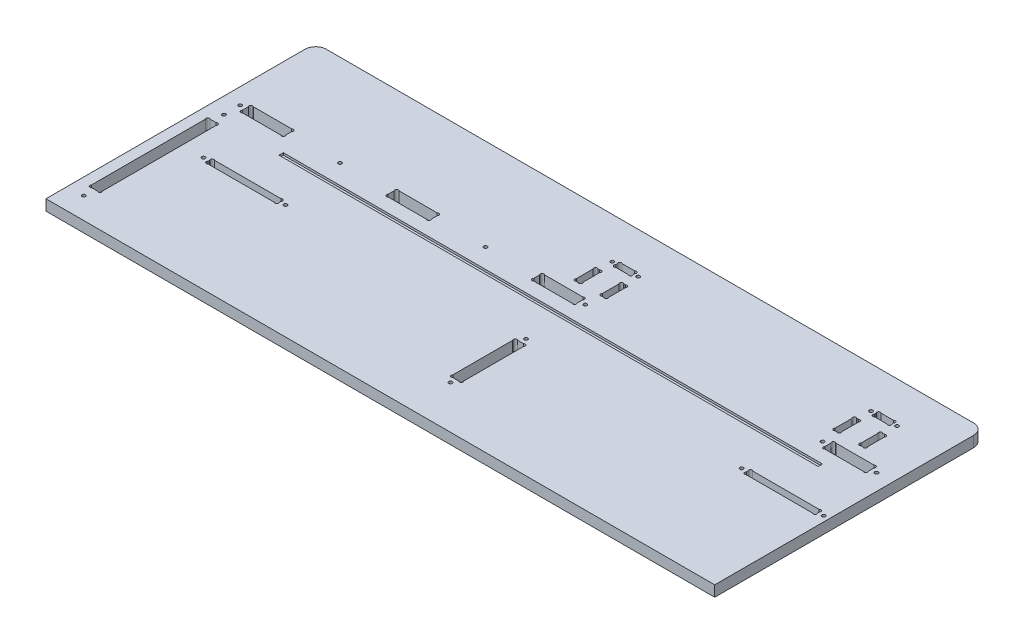
SolidWorks part; units mm, degrees
ref_plane "Plan de face" through (0, 0, 0) normal (0, 0, 1) x (1, 0, 0)
ref_plane "Plan de dessus" through (0, 0, 0) normal (0, 1, 0) x (1, 0, 0)
ref_plane "Plan de droite" through (0, 0, 0) normal (1, 0, 0) x (0, 0, -1)
sketch "Esquisse1" plane through (0, 0, 0) normal (0, 1, 0) x (1, 0, 0)
  line L0 (-55.9706, 0) -> (688.9813, 0) construction
  line L1 (0, -39.5787) -> (0, 380.8584) construction
  line L2 (-55.9706, 250) -> (688.9813, 250) construction
  line L3 (620, 380.8584) -> (620, -39.5787) construction
  line L4 (-21.2246, 170) -> (673.9823, 170) construction
  line L5 (340, 341.5482) -> (340, -24.8222) construction
  line L6 (673.9823, 160) -> (-21.2246, 160) construction
  line L7 (10, 341.5482) -> (10, -39.5787) construction
  line L8 (20, -39.5787) -> (20, 223.7385) construction
  line L9 (610, 341.5482) -> (610, 124.8557) construction
  line L10 (550, 341.5482) -> (550, 124.8557) construction
  line L11 (49.0204, 10) -> (-38.752, 10) construction
  line L12 (244.0085, 215) -> (592.9306, 215) construction
  line L13 (580, 280.9066) -> (580, 124.8557) construction
  line L14 (310, 280.9066) -> (310, 124.8557) construction
  line L15 (445, 234.3834) -> (445, 341.5482) construction
  line L16 (290.8762, 209) -> (347.4261, 209) construction
  line L17 (316, 236.8233) -> (316, 163.128) construction
  line L18 (334, 236.8233) -> (334, 163.128) construction
  line L19 (325, 257.541) -> (325, 197.6776) construction
  line L20 (313, 223.7385) -> (313, 205.81) construction
  line L21 (306.3451, 212) -> (359.8928, 212) construction
  line L22 (318.7842, 189.5) -> (359.8928, 189.5) construction
  line L23 (317, 223.7385) -> (317, 206.607) construction
  line L24 (306.3451, 179.5) -> (325, 179.5) construction
  line L25 (316, 179.5) -> (298.4851, 197.0149) construction
  line L26 (317, 211.2627) -> (317, 212.7373)
  line L27 (317, 215) -> (329.8508, 202.1492) construction
  line L28 (319.2627, 215) -> (330.7373, 215)
  line L29 (333, 211.2627) -> (333, 212.7373)
  line L30 (330.7373, 209) -> (319.2627, 209)
  line L31 (312.2627, 179.5) -> (313.7373, 179.5)
  line L32 (312.2627, 199.5) -> (313.7373, 199.5)
  line L33 (310, 197.2373) -> (310, 181.7627)
  line L34 (316, 181.7627) -> (316, 197.2373)
  line L35 (334, 181.7627) -> (334, 197.2373)
  line L36 (340, 197.2373) -> (340, 181.7627)
  line L37 (337.7373, 199.5) -> (336.2627, 199.5)
  line L38 (337.7373, 179.5) -> (336.2627, 179.5)
  line L39 (552.2627, 179.5) -> (553.7373, 179.5)
  line L40 (552.2627, 199.5) -> (553.7373, 199.5)
  line L41 (550, 197.2373) -> (550, 181.7627)
  line L42 (556, 181.7627) -> (556, 197.2373)
  line L43 (574, 181.7627) -> (574, 197.2373)
  line L44 (580, 197.2373) -> (580, 181.7627)
  line L45 (577.7373, 199.5) -> (576.2627, 199.5)
  line L46 (577.7373, 179.5) -> (576.2627, 179.5)
  line L47 (559.2627, 209) -> (570.7373, 209)
  line L48 (557, 211.2627) -> (557, 212.7373)
  line L49 (570.7373, 215) -> (559.2627, 215)
  line L50 (573, 211.2627) -> (573, 212.7373)
  line L51 (80.4661, 165) -> (624.1581, 165) construction
  line L52 (560, 174.5066) -> (560, 138.2607) construction
  line L53 (555, 174.5066) -> (555, 138.2607) construction
  line L54 (560, 160) -> (573.9521, 173.9521) construction
  line L55 (560, 167.7373) -> (560, 162.2627)
  line L56 (600, 167.7373) -> (600, 162.2627)
  line L57 (562.2627, 170) -> (597.7373, 170)
  line L58 (597.7373, 160) -> (562.2627, 160)
  line L59 (292.2627, 160) -> (327.7373, 160)
  line L60 (327.7373, 170) -> (292.2627, 170)
  line L61 (290, 167.7373) -> (290, 162.2627)
  line L62 (330, 167.7373) -> (330, 162.2627)
  line L63 (175, 313.2866) -> (175, 124.8557) construction
  line L64 (20, 167.7373) -> (20, 162.2627)
  line L65 (60, 167.7373) -> (60, 162.2627)
  line L66 (22.2627, 170) -> (57.7373, 170)
  line L67 (57.7373, 160) -> (22.2627, 160)
  line L68 (155, 179.5) -> (155, 124.8557) construction
  line L69 (155, 160) -> (177.234, 182.234) construction
  line L70 (155, 167.7373) -> (155, 162.2627)
  line L71 (195, 167.7373) -> (195, 162.2627)
  line L72 (157.2627, 170) -> (192.7373, 170)
  line L73 (192.7373, 160) -> (157.2627, 160)
  line L74 (242.5, 124.8557) -> (242.5, 179.5) construction
  line L75 (-16.8838, 85) -> (49.0204, 85) construction
  line L76 (10, 250) -> (610, 250)
  line L77 (0, 240) -> (0, 0)
  line L78 (0, 0) -> (620, 0)
  line L79 (620, 240) -> (620, 0)
  line L80 (28.427, 30) -> (-7.473, 30) construction
  line L81 (4.5525, 20) -> (28.427, 20) construction
  line L82 (15, 149.0553) -> (15, -13.6747) construction
  line L83 (20, 30) -> (-3.7272, 53.7272) construction
  line L84 (12.2627, 30) -> (17.7373, 30)
  line L85 (12.2627, 140) -> (17.7373, 140)
  line L86 (10, 137.7373) -> (10, 32.2627)
  line L87 (20, 32.2627) -> (20, 137.7373)
  line L88 (673.9823, 109) -> (-21.2246, 109) construction
  line L89 (673.9823, 103) -> (-21.2246, 103) construction
  line L90 (330, -24.8222) -> (330, 122.6364) construction
  line L91 (356.2719, 115) -> (325, 115) construction
  line L92 (356.2719, 35) -> (308.6408, 35) construction
  line L93 (335, 32.2627) -> (335, 82.0162) construction
  line L94 (345.0286, 75) -> (308.6408, 75) construction
  line L95 (345.0286, 45) -> (316, 45) construction
  line L96 (345.0286, 40) -> (333, 40) construction
  line L97 (330, 45) -> (340.0199, 55.0199) construction
  line L98 (337.7373, 45) -> (332.2627, 45)
  line L99 (337.7373, 105) -> (332.2627, 105)
  line L100 (340, 47.2627) -> (340, 102.7373)
  line L101 (330, 102.7373) -> (330, 47.2627)
  line L102 (35, 95.2987) -> (35, 134.8153) construction
  line L103 (327.5, -33.1463) -> (327.5, -9.4075) construction
  line L104 (577, 83.0157) -> (577, 115) construction
  line L105 (610, 83.0157) -> (610, 115) construction
  line L106 (641.1197, 106) -> (607.2136, 106) construction
  line L107 (615, 100.9312) -> (615, 118.2543) construction
  line L108 (610, 103) -> (596.866, 116.134) construction
  line L109 (610, 105.2627) -> (610, 106.7373)
  line L110 (544, 105.2627) -> (544, 106.7373)
  line L111 (607.7373, 103) -> (546.2627, 103)
  line L112 (546.2627, 109) -> (607.7373, 109)
  line L113 (108.7373, 109) -> (47.2627, 109)
  line L114 (47.2627, 103) -> (108.7373, 103)
  line L115 (111, 105.2627) -> (111, 106.7373)
  line L116 (45, 105.2627) -> (45, 106.7373)
  arc A0 (319.2627, 215) -> (317, 212.7373) centre (318.1314, 213.8686) ccw
  arc A1 (319.2627, 209) -> (317, 211.2627) centre (318.1314, 210.1314) cw
  arc A2 (330.7373, 209) -> (333, 211.2627) centre (331.8686, 210.1314) ccw
  arc A3 (330.7373, 215) -> (333, 212.7373) centre (331.8686, 213.8686) cw
  arc A4 (313.7373, 179.5) -> (316, 181.7627) centre (314.8686, 180.6314) ccw
  arc A5 (312.2627, 179.5) -> (310, 181.7627) centre (311.1314, 180.6314) cw
  arc A6 (312.2627, 199.5) -> (310, 197.2373) centre (311.1314, 198.3686) ccw
  arc A7 (313.7373, 199.5) -> (316, 197.2373) centre (314.8686, 198.3686) cw
  arc A8 (336.2627, 179.5) -> (334, 181.7627) centre (335.1314, 180.6314) cw
  arc A9 (336.2627, 199.5) -> (334, 197.2373) centre (335.1314, 198.3686) ccw
  arc A10 (337.7373, 199.5) -> (340, 197.2373) centre (338.8686, 198.3686) cw
  arc A11 (337.7373, 179.5) -> (340, 181.7627) centre (338.8686, 180.6314) ccw
  arc A12 (552.2627, 179.5) -> (550, 181.7627) centre (551.1314, 180.6314) cw
  arc A13 (552.2627, 199.5) -> (550, 197.2373) centre (551.1314, 198.3686) ccw
  arc A14 (553.7373, 199.5) -> (556, 197.2373) centre (554.8686, 198.3686) cw
  arc A15 (553.7373, 179.5) -> (556, 181.7627) centre (554.8686, 180.6314) ccw
  arc A16 (576.2627, 199.5) -> (574, 197.2373) centre (575.1314, 198.3686) ccw
  arc A17 (577.7373, 199.5) -> (580, 197.2373) centre (578.8686, 198.3686) cw
  arc A18 (577.7373, 179.5) -> (580, 181.7627) centre (578.8686, 180.6314) ccw
  arc A19 (576.2627, 179.5) -> (574, 181.7627) centre (575.1314, 180.6314) cw
  arc A20 (559.2627, 215) -> (557, 212.7373) centre (558.1314, 213.8686) ccw
  arc A21 (559.2627, 209) -> (557, 211.2627) centre (558.1314, 210.1314) cw
  arc A22 (570.7373, 209) -> (573, 211.2627) centre (571.8686, 210.1314) ccw
  arc A23 (570.7373, 215) -> (573, 212.7373) centre (571.8686, 213.8686) cw
  circle A24 centre (313, 212) radius 1.6
  circle A25 centre (337, 212) radius 1.6
  circle A26 centre (553, 212) radius 1.6
  circle A27 centre (577, 212) radius 1.6
  circle A28 centre (555, 165) radius 1.6
  arc A29 (560, 162.2627) -> (562.2627, 160) centre (561.1314, 161.1314) ccw
  arc A30 (560, 167.7373) -> (562.2627, 170) centre (561.1314, 168.8686) cw
  arc A31 (600, 167.7373) -> (597.7373, 170) centre (598.8686, 168.8686) ccw
  arc A32 (600, 162.2627) -> (597.7373, 160) centre (598.8686, 161.1314) cw
  circle A33 centre (605, 165) radius 1.6
  arc A34 (290, 162.2627) -> (292.2627, 160) centre (291.1314, 161.1314) ccw
  arc A35 (290, 167.7373) -> (292.2627, 170) centre (291.1314, 168.8686) cw
  arc A36 (330, 167.7373) -> (327.7373, 170) centre (328.8686, 168.8686) ccw
  arc A37 (330, 162.2627) -> (327.7373, 160) centre (328.8686, 161.1314) cw
  circle A38 centre (335, 165) radius 1.6
  circle A39 centre (15, 165) radius 1.6
  arc A40 (20, 162.2627) -> (22.2627, 160) centre (21.1314, 161.1314) ccw
  arc A41 (20, 167.7373) -> (22.2627, 170) centre (21.1314, 168.8686) cw
  arc A42 (60, 167.7373) -> (57.7373, 170) centre (58.8686, 168.8686) ccw
  arc A43 (60, 162.2627) -> (57.7373, 160) centre (58.8686, 161.1314) cw
  arc A44 (155, 162.2627) -> (157.2627, 160) centre (156.1314, 161.1314) ccw
  arc A45 (155, 167.7373) -> (157.2627, 170) centre (156.1314, 168.8686) cw
  arc A46 (195, 162.2627) -> (192.7373, 160) centre (193.8686, 161.1314) cw
  arc A47 (195, 167.7373) -> (192.7373, 170) centre (193.8686, 168.8686) ccw
  circle A48 centre (242.5, 165) radius 1.6
  circle A49 centre (107.5, 165) radius 1.6
  arc A50 (17.7373, 30) -> (20, 32.2627) centre (18.8686, 31.1314) ccw
  circle A51 centre (15, 20) radius 1.6
  arc A52 (12.2627, 30) -> (10, 32.2627) centre (11.1314, 31.1314) cw
  arc A53 (17.7373, 140) -> (20, 137.7373) centre (18.8686, 138.8686) cw
  arc A54 (12.2627, 140) -> (10, 137.7373) centre (11.1314, 138.8686) ccw
  circle A55 centre (15, 150) radius 1.6
  arc A56 (10, 250) -> (0, 240) centre (10, 240) ccw
  arc A57 (610, 250) -> (620, 240) centre (610, 240) cw
  circle A58 centre (335, 40) radius 1.6
  arc A59 (330, 47.2627) -> (332.2627, 45) centre (331.1314, 46.1314) ccw
  arc A60 (340, 47.2627) -> (337.7373, 45) centre (338.8686, 46.1314) cw
  arc A61 (330, 102.7373) -> (332.2627, 105) centre (331.1314, 103.8686) cw
  arc A62 (340, 102.7373) -> (337.7373, 105) centre (338.8686, 103.8686) ccw
  circle A63 centre (335, 110) radius 1.6
  arc A64 (607.7373, 103) -> (610, 105.2627) centre (608.8686, 104.1314) ccw
  circle A65 centre (615, 106) radius 1.6
  arc A66 (607.7373, 109) -> (610, 106.7373) centre (608.8686, 107.8686) cw
  circle A67 centre (539, 106) radius 1.6
  arc A68 (546.2627, 109) -> (544, 106.7373) centre (545.1314, 107.8686) ccw
  arc A69 (546.2627, 103) -> (544, 105.2627) centre (545.1314, 104.1314) cw
  arc A70 (108.7373, 103) -> (111, 105.2627) centre (109.8686, 104.1314) ccw
  arc A71 (108.7373, 109) -> (111, 106.7373) centre (109.8686, 107.8686) cw
  circle A72 centre (116, 106) radius 1.6
  arc A73 (47.2627, 109) -> (45, 106.7373) centre (46.1314, 107.8686) ccw
  circle A74 centre (40, 106) radius 1.6
  arc A75 (47.2627, 103) -> (45, 105.2627) centre (46.1314, 104.1314) cw
  dimension "D25" = 5
  dimension "D28" = 45
  dimension "D29" = 165
  dimension "D32" = 47.5
  dimension "D33" = 10
  dimension "D39" = 10
  dimension "D49" = 45
  dimension "D50" = 15
  dimension "D1" = 250
  dimension "D2" = 620
  dimension "D3" = 10
  dimension "D4" = 80
  dimension "D5" = 10
  dimension "D6" = 10
  dimension "D7" = 330
  dimension "D8" = 30
  dimension "D9" = 10
  dimension "D10" = 60
  dimension "D11" = 105
  dimension "D12" = 45
  dimension "D13" = 30
  dimension "D14" = 15
  dimension "D15" = 6
  dimension "D16" = 6
  dimension "D17" = 6
  dimension "D18" = 3
  dimension "D19" = 3
  dimension "D20" = 19.5
  dimension "D21" = 8
  dimension "D22" = 10
  dimension "D23" = 45
  dimension "D24" = 45
  dimension "D26" = 20
  dimension "D27" = 5
  dimension "D30" = 20
  dimension "D31" = 45
  dimension "D34" = 75
  dimension "D35" = 5
  dimension "D36" = 10
  dimension "D37" = 10
  dimension "D38" = 45
  dimension "D40" = 51
  dimension "D41" = 10
  dimension "D42" = 6
  dimension "D43" = 80
  dimension "D44" = 45
  dimension "D45" = 5
  dimension "D46" = 10
  dimension "D47" = 40
  dimension "D48" = 5
  dimension "D51" = 292.5
  dimension "D52" = 10
  dimension "D53" = 43
  dimension "D54" = 3
  dimension "D55" = 5
  dimension "D56" = 45
extrude "Extrusion1" add sketch "Esquisse1" along normal blind 10
sketch "Esquisse2" plane through (0, 10, 0) normal (0, 1, 0) x (-1, 0, 0)
  line L0 (-419.8742, -160) -> (13.7839, -160) construction
  line L1 (-582.3746, -147) -> (4.5674, -147) construction
  line L2 (-573, -120.1449) -> (-573, -151.1898) construction
  line L3 (-73, -120.1449) -> (-73, -151.1898) construction
  line L4 (-582.3746, -143) -> (4.5674, -143) construction
  line L5 (-620, 21.4973) -> (-620, -261.3021) construction
  line L7 (-573, -143) -> (-73, -143)
  line L8 (-573, -143) -> (-573, -147)
  line L9 (-573, -147) -> (-73, -147)
  line L10 (-73, -143) -> (-73, -147)
  dimension "D1" = 13
  dimension "D2" = 4
  dimension "D3" = 47
  dimension "D4" = 500
extrude "Enlèv. mat.-Extru.1" cut sketch "Esquisse2" against normal blind 2
